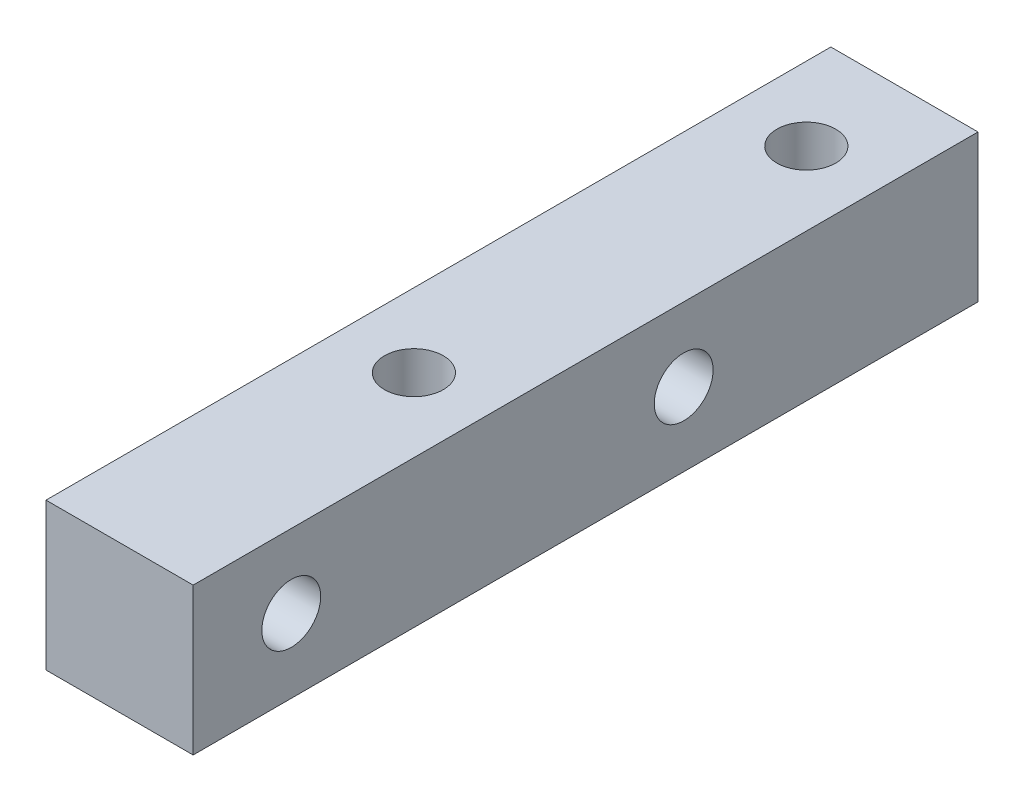
SolidWorks part; units mm, degrees
material "6061-T6 (SS)"
ref_plane "前视基准面" through (0, 0, 0) normal (0, 0, 1) x (1, 0, 0)
ref_plane "上视基准面" through (0, 0, 0) normal (0, 1, 0) x (1, 0, 0)
ref_plane "右视基准面" through (0, 0, 0) normal (1, 0, 0) x (0, 0, -1)
sketch "草图1" plane through (0, 0, 0) normal (0, 0, 1) x (1, 0, 0)
  line L1 (0, 0) -> (6, 0)
  line L2 (0, 0) -> (0, 6)
  line L3 (0, 6) -> (6, 6)
  line L4 (6, 0) -> (6, 6)
  dimension "D1" = 6
  dimension "D2" = 6
extrude "凸台-拉伸1" add sketch "草图1" along normal blind 32
sketch "草图2" plane through (0, 6, 0) normal (0, 1, 0) x (1, 0, 0)
  line L0 (3, 0) -> (3, -4) construction
  line L1 (6, 0) -> (0, 0) construction
  line L2 (3, -4) -> (3, -20) construction
  circle A0 centre (3, -4) radius 1.2
  circle A1 centre (3, -20) radius 1.2
  dimension "D1" = 2.4
  dimension "D2" = 4
  dimension "D3" = 16
extrude "切除-拉伸1" cut sketch "草图2" against normal blind 50
cosmetic thread "装饰螺纹线5" parameters "D2"=3
cosmetic thread "装饰螺纹线6" parameters "D2"=3
sketch "草图3" plane through (0, 0, 0) normal (-1, 0, 0) x (0, 0, 1)
  line L0 (0, 3) -> (12, 3) construction
  line L1 (0, 6) -> (0, 0) construction
  line L2 (12, 3) -> (28, 3) construction
  circle A0 centre (28, 3) radius 1.2
  circle A1 centre (12, 3) radius 1.2
  dimension "D3" = 2.4
  dimension "D1" = 12
  dimension "D2" = 16
extrude "切除-拉伸2" cut sketch "草图3" against normal blind 50
cosmetic thread "装饰螺纹线7" parameters "D2"=3
cosmetic thread "装饰螺纹线8" parameters "D2"=3
